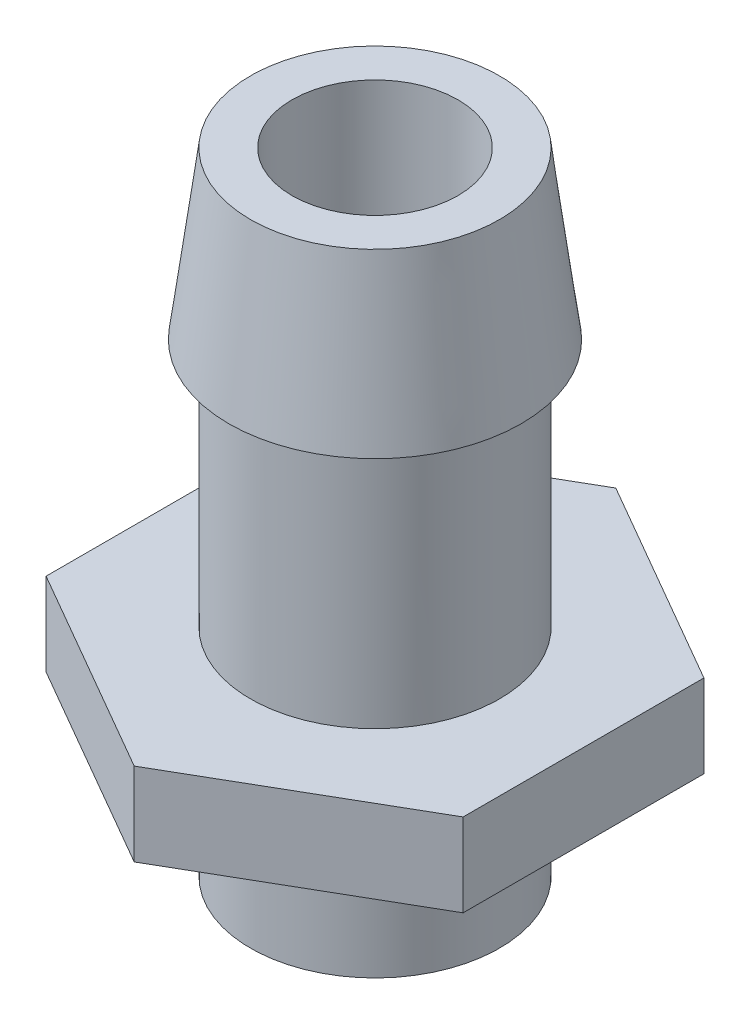
SolidWorks part; units mm, degrees
material "1060 Alloy"
ref_plane "Front Plane" through (0, 0, 0) normal (0, 0, 1) x (1, 0, 0)
ref_plane "Top Plane" through (0, 0, 0) normal (0, 1, 0) x (1, 0, 0)
ref_plane "Right Plane" through (0, 0, 0) normal (1, 0, 0) x (0, 0, -1)
sketch "Sketch1" plane through (0, 0, 0) normal (0, 1, 0) x (1, 0, 0)
  circle A0 centre (0, 0) radius 4.7625
  circle A1 centre (0, 0) radius 3.175
extrude "Extrude1" add sketch "Sketch1" along normal blind 15.875
sketch "Sketch2" plane through (0, 0, 0) normal (0, -1, 0) x (1, 0, 0)
  line L0 (0, 9.2075) -> (0, -9.2075) construction
  line L1 (7.9739, 4.6037) -> (7.9739, -4.6037)
  line L2 (0, 9.2075) -> (7.9739, 4.6037)
  line L3 (0, -9.2075) -> (7.9739, -4.6037)
  line L4 (0, -9.2075) -> (-7.9739, -4.6037)
  line L5 (0, 9.2075) -> (-7.9739, 4.6037)
  line L6 (-7.9739, 4.6037) -> (-7.9739, -4.6037)
  circle A0 centre (0, 0) radius 3.175
  dimension "D1" = 9.2075
  dimension "D2" = 9.2075
  dimension "D3" = 9.2075
extrude "Extrude2" add sketch "Sketch2" along normal blind 3.175
sketch "Sketch3" plane through (0, -3.175, 0) normal (0, -1, 0) x (1, 0, 0)
  circle A0 centre (0, 0) radius 3.175
  circle A1 centre (0, 0) radius 4.7625
extrude "Extrude3" add sketch "Sketch3" along normal blind 5.08
sketch "Sketch4" plane through (0, -3.175, 0) normal (0, -1, 0) x (1, 0, 0)
  circle A0 centre (0, 0) radius 4.7625
  circle A1 centre (0, 0) radius 6.35
extrude "Cut-Extrude1" cut sketch "Sketch4" against normal blind 1.5875
sketch "Sketch5" plane through (0, 15.875, 0) normal (0, 1, 0) x (-1, 0, 0)
  circle A0 centre (0, 0) radius 4.7625
  circle A1 centre (0, 0) radius 5.588
extrude "Extrude4" add sketch "Sketch5" against normal blind 6.35
sketch "Sketch7" plane through (0, 0, 0) normal (1, 0, 0) x (0, 0, -1)
  line L0 (-5.588, 9.525) -> (-4.7625, 15.875)
  line L1 (5.588, 15.875) -> (-5.588, 15.875) construction
  line L2 (0, 15.875) -> (0, 0) construction
  line L3 (-4.7625, 15.875) -> (-5.588, 15.875)
  line L4 (-5.588, 15.875) -> (-5.588, 9.525)
  dimension "D1" = 0.8255
revolve "Cut-Revolve1" cut sketch "Sketch7" angle 360 about L2
